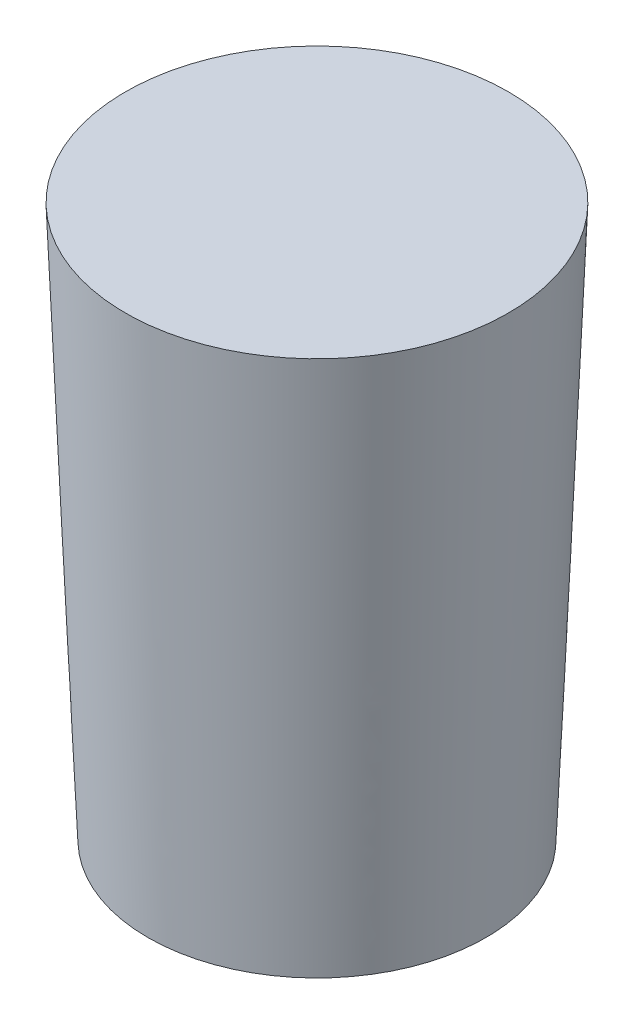
SolidWorks part; units mm, degrees
ref_plane "Přední rovina" through (0, 0, 0) normal (0, 0, 1) x (1, 0, 0)
ref_plane "Horní rovina" through (0, 0, 0) normal (0, 1, 0) x (1, 0, 0)
ref_plane "Pravá rovina" through (0, 0, 0) normal (1, 0, 0) x (0, 0, -1)
sketch "Skica1" plane through (0, 0, 0) normal (0, 0, 1) x (1, 0, 0)
  line L0 (0, 0) -> (0, 94)
  line L1 (0, 94) -> (-34, 94)
  arc A1 (-30, -4) -> (0, 0) centre (4.7234, -149.9256) cw
  spline S0 degree 2 poles (-30, -4) (-32.096, 44.9961) (-34, 94) knots 0 0 0 1 1 1
  point P7 (-32.15, 47.5)
  point P10 (-34, 94)
  dimension "D7" = 150
  dimension "D1" = 4
  dimension "D2" = 30
  dimension "D3" = 98
  dimension "D4" = 34
  dimension "D5" = 51.5
  dimension "D6" = 32.15
revolve "Rotovat1" add sketch "Skica1" angle 360 about L0
equation "\"PPlocha [mm2] - > [dm2]\"= \"Plocha\" / 10000"
